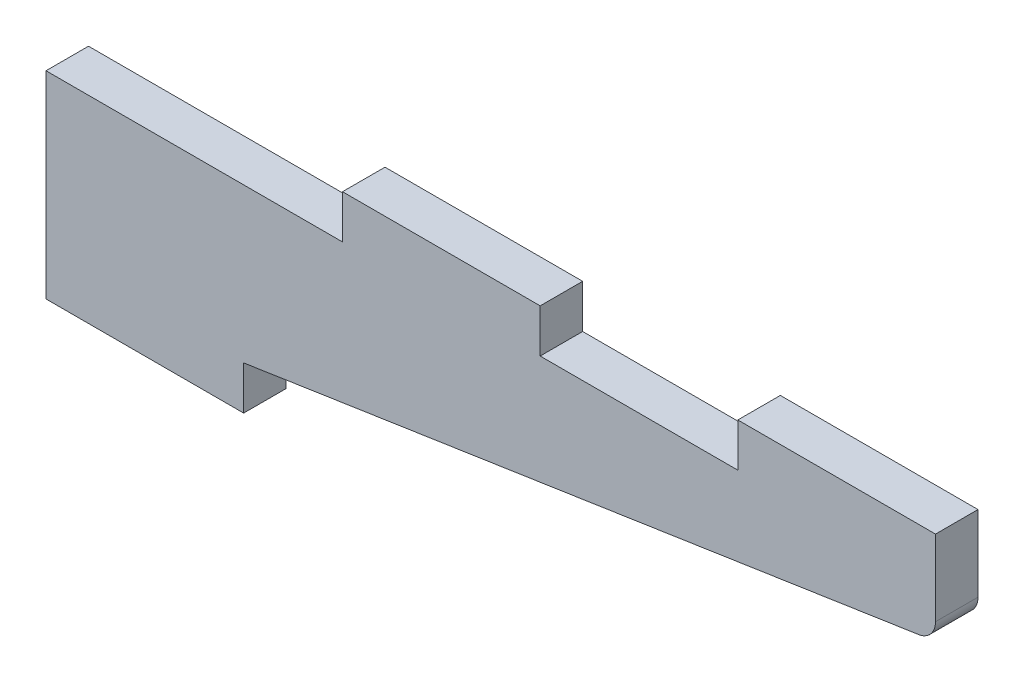
SolidWorks part; units mm, degrees
material "Acrylic (Medium-high impact)"
ref_plane "Front Plane" through (0, 0, 0) normal (0, 0, 1) x (1, 0, 0)
ref_plane "Top Plane" through (0, 0, 0) normal (0, 1, 0) x (1, 0, 0)
ref_plane "Right Plane" through (0, 0, 0) normal (1, 0, 0) x (0, 0, -1)
sketch "Sketch1" plane through (0, 0, 0) normal (0, 0, 1) x (1, 0, 0)
  line L0 (0, 0) -> (0, 25.4)
  line L1 (0, 25.4) -> (38.1, 25.4)
  line L2 (38.1, 25.4) -> (38.1, 30.988)
  line L3 (38.1, 30.988) -> (63.5, 30.988)
  line L4 (63.5, 30.988) -> (63.5, 25.4)
  line L5 (63.5, 25.4) -> (88.9, 25.4)
  line L6 (88.9, 25.4) -> (88.9, 30.988)
  line L7 (88.9, 30.988) -> (114.3, 30.988)
  line L8 (114.3, 30.988) -> (114.3, 25.4)
  line L9 (0, 0) -> (25.4, 0)
  line L10 (114.3, 19.05) -> (114.3, 25.4)
  line L11 (25.4, 0) -> (25.4, 5.588)
  line L12 (25.4, 5.588) -> (114.3, 19.05)
  dimension "D1" = 6.35
  dimension "D2" = 25.4
  dimension "D3" = 5.588
  dimension "D4" = 38.1
  dimension "D5" = 25.4
  dimension "D6" = 50.8
extrude "Boss-Extrude1" add sketch "Sketch1" along normal blind 5.461
fillet "Fillet1" radius 2.54 1 edges at (114.3, 19.05, 2.7305)
